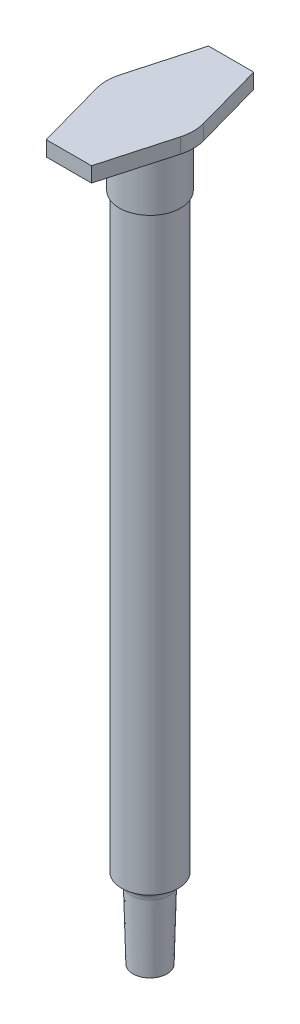
SolidWorks part; units mm, degrees
material "PET"
ref_plane "Front Plane" through (0, 0, 0) normal (0, 0, 1) x (1, 0, 0)
ref_plane "Top Plane" through (0, 0, 0) normal (0, 1, 0) x (1, 0, 0)
ref_plane "Right Plane" through (0, 0, 0) normal (1, 0, 0) x (0, 0, -1)
sketch "Sketch1" plane through (0, 0, 0) normal (0, 1, 0) x (1, 0, 0)
  circle A0 centre (0, 0) radius 3.325
  dimension "D1" = 6.65
extrude "Boss-Extrude1" add sketch "Sketch1" along normal blind 69.2
sketch "Sketch2" plane through (0, 69.2, 0) normal (0, 1, 0) x (1, 0, 0)
  circle A0 centre (0, 0) radius 3.59
  dimension "D1" = 7.18
extrude "Boss-Extrude2" add sketch "Sketch2" along normal blind 6.82
sketch "Sketch3" plane through (0, 76.02, 0) normal (0, 1, 0) x (1, 0, 0)
  line L0 (-4.9177, 1.37) -> (-2.65, 9.51)
  line L1 (-2.65, 9.51) -> (2.65, 9.51)
  line L2 (2.65, 9.51) -> (4.9177, 1.37)
  line L3 (0, 0) -> (0, 9.51) construction
  line L4 (-5.105, 0) -> (5.105, 0) construction
  line L5 (2.65, -9.51) -> (4.9177, -1.37)
  line L6 (-2.65, -9.51) -> (2.65, -9.51)
  line L7 (-4.9177, -1.37) -> (-2.65, -9.51)
  arc A0 (-4.9177, 1.37) -> (-4.9177, -1.37) centre (0, 0) ccw
  arc A1 (4.9177, -1.37) -> (4.9177, 1.37) centre (0, 0) ccw
  dimension "D1" = 10.21
  dimension "D2" = 5.3
  dimension "D3" = 19.02
extrude "Boss-Extrude3" add sketch "Sketch3" along normal blind 1.76
sketch "Sketch4" plane through (0, 0, 0) normal (1, 0, 0) x (0, 0, -1)
  line L0 (0, 0) -> (0, -9.35)
  line L1 (0, -9.35) -> (2, -9.35)
  line L2 (2, -9.35) -> (2.21, -1.3)
  line L3 (3.325, 0) -> (0, 0)
  arc A0 (2.21, -1.3) -> (3.325, 0) centre (3.5666, -1.3354) cw
  dimension "D1" = 9.35
  dimension "D2" = 2
  dimension "D3" = 2.21
  dimension "D4" = 1.3
revolve "Revolve1" add sketch "Sketch4" angle 360 about L0
